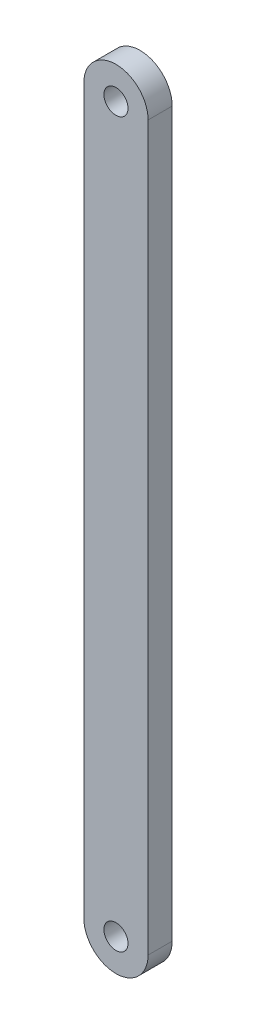
SolidWorks part; units mm, degrees
ref_plane "前视基准面" through (0, 0, 0) normal (0, 0, 1) x (1, 0, 0)
ref_plane "上视基准面" through (0, 0, 0) normal (0, 1, 0) x (1, 0, 0)
ref_plane "右视基准面" through (0, 0, 0) normal (1, 0, 0) x (0, 0, -1)
sketch "草图1" plane through (0, 0, 0) normal (0, 0, 1) x (1, 0, 0)
  line L1 (-4, 45) -> (4, 45)
  line L2 (-4, 45) -> (-4, -45)
  line L3 (-4, -45) -> (4, -45)
  line L4 (4, 45) -> (4, -45)
  line L5 (-4, 45) -> (4, -45) construction
  line L6 (-4, -45) -> (4, 45) construction
  point P0 (0, 0)
  dimension "D1" = 90
  dimension "D2" = 8
extrude "凸台-拉伸1" add sketch "草图1" along normal blind 3
sketch "草图2" plane through (0, 0, 0) normal (0, 0, 1) x (1, 0, 0)
  line L0 (4, 45) -> (-4, 45) construction
  line L1 (-4, -45) -> (4, -45) construction
  circle A0 centre (0, 45) radius 4
  circle A1 centre (0, -45) radius 4
extrude "凸台-拉伸2" add sketch "草图2" along normal blind 3
sketch "草图3" plane through (0, 0, 3) normal (0, 0, 1) x (1, 0, 0)
  circle A0 centre (0, 45) radius 1.5
  circle A1 centre (0, -45) radius 1.5
  dimension "D1" = 3
  dimension "D2" = 3
extrude "切除-拉伸1" cut sketch "草图3" against normal blind 3
